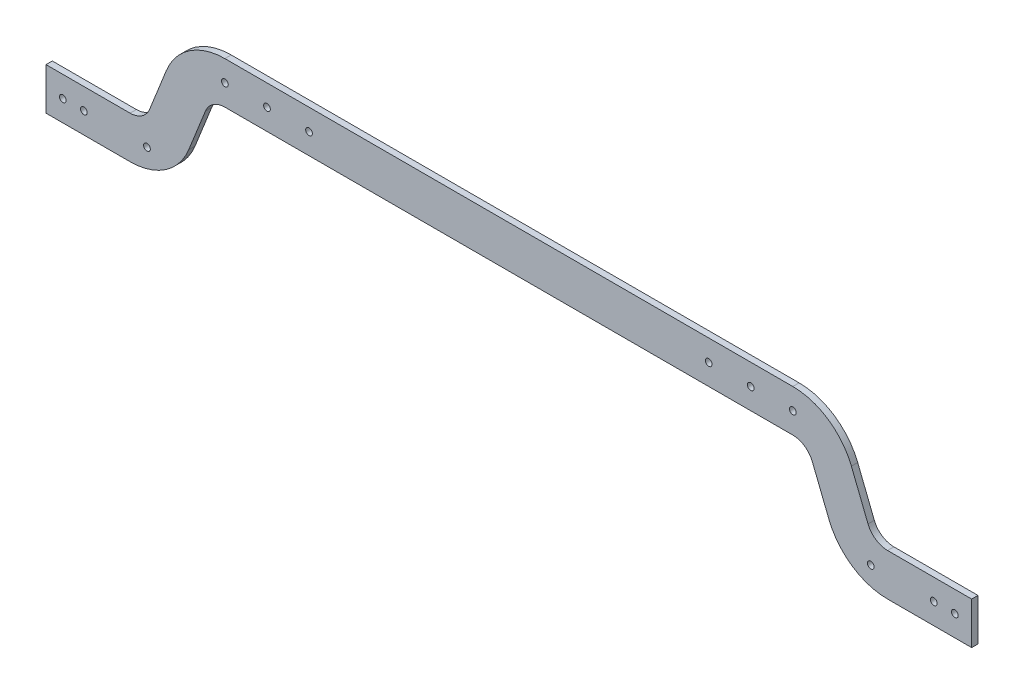
SolidWorks part; units mm, degrees
material "Thornel Mat VMA"
ref_plane "Front Plane" through (0, 0, 0) normal (0, 0, 1) x (1, 0, 0)
ref_plane "Top Plane" through (0, 0, 0) normal (0, 1, 0) x (1, 0, 0)
ref_plane "Right Plane" through (0, 0, 0) normal (1, 0, 0) x (0, 0, -1)
sketch "Sketch1" plane through (0, 0, 0) normal (0, 0, 1) x (1, 0, 0)
  line L0 (-592.497, 145) -> (-452.497, 145) construction
  line L1 (-512.5556, 145) -> (-472.5556, 145)
  line L2 (-512.5556, 145) -> (-512.5556, 165)
  line L3 (-512.5556, 165) -> (-472.5556, 165)
  line L5 (-452.497, 165) -> (-592.497, 165) construction
  line L6 (-592.497, 165) -> (7.503, 165) construction
  line L7 (-292.497, 165) -> (-292.497, 190.002) construction
  line L8 (-455.3628, 191.1151) -> (-463.267, 171.2956)
  line L9 (-157.497, 210.002) -> (-427.497, 210.002)
  line L11 (-157.497, 190.002) -> (-427.497, 190.002)
  line L13 (-436.7856, 183.7064) -> (-444.6898, 163.8869)
  line L14 (-292.497, 210.002) -> (-292.497, 242.7169) construction
  line L15 (-148.2085, 183.7064) -> (-140.3043, 163.8869)
  line L16 (-129.6313, 191.1151) -> (-121.7271, 171.2956)
  line L17 (-72.4385, 165) -> (-112.4385, 165)
  line L18 (-72.4385, 145) -> (-72.4385, 165)
  line L19 (-72.4385, 145) -> (-112.4385, 145)
  arc A0 (-427.497, 210.002) -> (-455.3628, 191.1151) centre (-427.497, 180.002) ccw
  arc A1 (-472.5556, 165) -> (-463.267, 171.2956) centre (-472.5556, 175) ccw
  arc A2 (-427.497, 190.002) -> (-436.7856, 183.7064) centre (-427.497, 180.002) ccw
  arc A3 (-472.5556, 145) -> (-444.6898, 163.8869) centre (-472.5556, 175) ccw
  arc A4 (-112.4385, 145) -> (-140.3043, 163.8869) centre (-112.4385, 175) cw
  arc A5 (-157.497, 190.002) -> (-148.2085, 183.7064) centre (-157.497, 180.002) cw
  arc A6 (-112.4385, 165) -> (-121.7271, 171.2956) centre (-112.4385, 175) cw
  arc A7 (-157.497, 210.002) -> (-129.6313, 191.1151) centre (-157.497, 180.002) cw
  dimension "D1" = 10
  dimension "D3" = 10
  dimension "D2" = 20
  dimension "D4" = 135
  dimension "D5" = 40
extrude "Extrude1" add sketch "Sketch1" along normal blind 3
sketch "Sketch2" plane through (0, 0, 3) normal (0, 0, 1) x (1, 0, 0)
  line L0 (-512.5556, 155) -> (-72.4385, 155) construction
  line L1 (-512.5556, 165) -> (-512.5556, 145) construction
  line L2 (-472.5556, 165) -> (-472.5556, 145) construction
  line L3 (-72.4385, 145) -> (-72.4385, 165) construction
  line L4 (-292.497, 155) -> (-292.497, 244.3351) construction
  line L5 (-427.497, 210.002) -> (-427.497, 190.002) construction
  line L6 (-427.497, 200.002) -> (-292.497, 199.6675) construction
  line L7 (-157.497, 210.002) -> (-157.497, 190.002) construction
  line L8 (-112.4385, 165) -> (-112.4385, 145) construction
  circle A0 centre (-494.5556, 155) radius 1.6
  circle A1 centre (-464.5556, 155) radius 1.6
  circle A2 centre (-427.497, 200.002) radius 1.6
  circle A3 centre (-407.497, 199.9525) radius 1.6
  circle A4 centre (-387.497, 199.9029) radius 1.6
  circle A5 centre (-504.5556, 155) radius 1.6
  circle A6 centre (-80.4385, 155) radius 1.6
  circle A7 centre (-197.497, 199.9029) radius 1.6
  circle A8 centre (-177.497, 199.9525) radius 1.6
  circle A9 centre (-157.497, 200.002) radius 1.6
  circle A10 centre (-120.4385, 155) radius 1.6
  circle A11 centre (-90.4385, 155) radius 1.6
  dimension "D1" = 3.2
  dimension "D2" = 8
  dimension "D3" = 10
  dimension "D4" = 30
  dimension "D5" = 20
  dimension "D6" = 20
extrude "Cut-Extrude1" cut sketch "Sketch2" against normal blind 3
